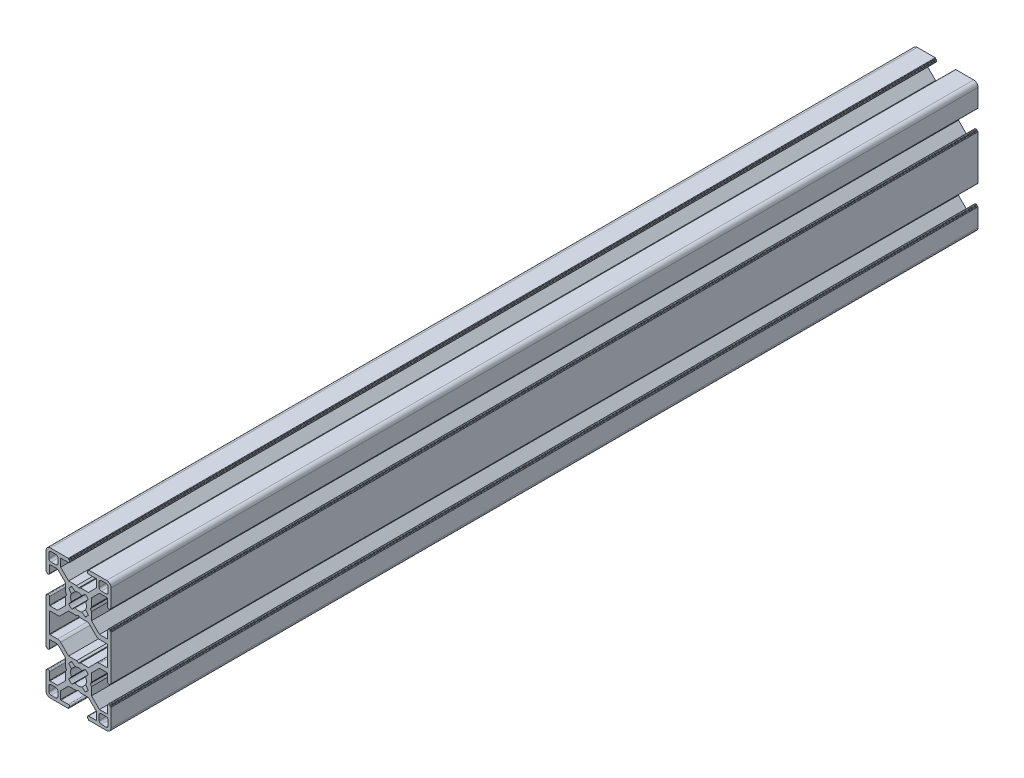
SolidWorks part; units mm, degrees
ref_plane "Спереди" through (0, 0, 0) normal (0, 0, 1) x (1, 0, 0)
ref_plane "Сверху" through (0, 0, 0) normal (0, 1, 0) x (1, 0, 0)
ref_plane "Справа" through (0, 0, 0) normal (1, 0, 0) x (0, 0, -1)
sketch "Эскиз1" plane through (0, 0, 0) normal (0, 0, 1) x (1, 0, 0)
  line L0 (13.4477, 10.8313) -> (13.4477, 8.6313)
  line L1 (10.2477, 7.6313) -> (12.4477, 7.6313)
  line L2 (9.2477, 10.8313) -> (9.2477, 8.6313)
  line L3 (10.2477, 11.8313) -> (12.4477, 11.8313)
  line L4 (2.8836, 2.6497) -> (1.3478, 1.4119)
  line L5 (3.0283, -0.2685) -> (4.2531, 1.286)
  line L6 (5.7522, -0.9686) -> (5.2326, -1.8687)
  line L7 (5.7522, 2.7216) -> (5.7522, -0.9686)
  line L8 (-0.2523, -7.3535) -> (0.6477, -7.8687)
  line L9 (0.6477, -7.8687) -> (4.3335, -7.8687)
  line L15 (14.7477, -27.1187) -> (14.7477, -6.6187)
  line L16 (14.4477, -6.4187) -> (14.5477, -6.4187)
  line L17 (14.2477, -6.2187) -> (14.2477, -6.1187)
  line L18 (13.6977, -5.9187) -> (14.0477, -5.9187)
  line L19 (12.8977, -10.1187) -> (9.4119, -10.1187)
  line L20 (5.7522, -6.4589) -> (5.7522, -2.7687)
  line L21 (5.7522, -2.7687) -> (5.2326, -1.8687)
  line L22 (12.8977, 6.3813) -> (9.4119, 6.3814)
  line L23 (13.6977, 2.1813) -> (14.0477, 2.1813)
  line L24 (14.2477, 2.4813) -> (14.2477, 2.3813)
  line L25 (14.4477, 2.6813) -> (14.5477, 2.6813)
  line L26 (14.7477, 11.1313) -> (14.7477, 2.8813)
  line L27 (4.4977, 13.1313) -> (12.7477, 13.1313)
  line L28 (4.2977, 12.9313) -> (4.2977, 12.8313)
  line L29 (3.9977, 12.6313) -> (4.0977, 12.6313)
  line L30 (3.7977, 12.4313) -> (3.7977, 12.0813)
  line L31 (7.9977, 7.7956) -> (7.9977, 11.2813)
  line L32 (0.6477, 4.1313) -> (4.3335, 4.1313)
  line L33 (-0.2523, 3.6162) -> (0.6477, 4.1313)
  line L38 (-3.3882, -6.3871) -> (-1.8524, -5.1492)
  line L39 (-3.5328, -3.4688) -> (-4.7576, -5.0233)
  line L40 (-0.2523, 3.6162) -> (-1.1523, 4.1313)
  line L41 (-1.1523, 4.1313) -> (-4.8381, 4.1313)
  line L42 (-8.5023, 7.7956) -> (-8.5023, 11.2813)
  line L43 (-4.3023, 12.4313) -> (-4.3023, 12.0813)
  line L44 (-4.5023, 12.6313) -> (-4.6023, 12.6313)
  line L45 (-4.8023, 12.9313) -> (-4.8023, 12.8313)
  line L46 (-5.0023, 13.1313) -> (-13.2523, 13.1313)
  line L47 (-15.2523, 11.1313) -> (-15.2523, 2.8813)
  line L48 (-14.9523, 2.6813) -> (-15.0523, 2.6813)
  line L49 (-14.7523, 2.4813) -> (-14.7523, 2.3813)
  line L50 (-14.2023, 2.1813) -> (-14.5523, 2.1813)
  line L51 (-13.4023, 6.3813) -> (-9.9165, 6.3813)
  line L52 (-6.2567, -2.7687) -> (-5.7371, -1.8687)
  line L53 (-6.2568, -6.4589) -> (-6.2567, -2.7687)
  line L54 (-13.4023, -10.1187) -> (-9.9165, -10.1187)
  line L55 (-14.2023, -5.9187) -> (-14.5523, -5.9187)
  line L56 (-14.7523, -6.2187) -> (-14.7523, -6.1187)
  line L57 (-14.9523, -6.4187) -> (-15.0523, -6.4187)
  line L58 (-15.2523, -27.1187) -> (-15.2523, -6.6187)
  line L63 (3.0283, -3.4688) -> (4.2531, -5.0233)
  line L64 (2.8836, -6.3871) -> (1.3478, -5.1492)
  line L66 (-1.1523, -7.8687) -> (-4.8381, -7.8687)
  line L67 (-0.2523, -7.3535) -> (-1.1523, -7.8687)
  line L72 (-6.2568, 2.7216) -> (-6.2567, -0.9686)
  line L73 (-6.2567, -0.9686) -> (-5.7371, -1.8687)
  line L74 (-3.5328, -0.2685) -> (-4.7576, 1.286)
  line L75 (-3.3882, 2.6497) -> (-1.8524, 1.4119)
  line L76 (-10.7523, 11.8313) -> (-12.9523, 11.8313)
  line L77 (-9.7523, 10.8313) -> (-9.7523, 8.6313)
  line L78 (-10.7523, 7.6313) -> (-12.9523, 7.6313)
  line L79 (-13.9523, 10.8313) -> (-13.9523, 8.6313)
  line L80 (-23.7379, -1.8687) -> (20.6785, -1.8687) construction
  line L81 (-0.2523, 16.0876) -> (-0.2523, -7.3535) construction
  line L82 (25.0447, 11.4813) -> (-23.082, 11.4813) construction
  line L83 (-4.9023, 11.4813) -> (-8.3023, 11.4813)
  line L84 (4.3977, 11.4813) -> (7.7977, 11.4813)
  line L85 (-6.4795, 6.1563) -> (-9.3562, 3.2829) construction
  line L88 (-0.2523, -1.8687) -> (-27.0655, 24.9445) construction
  line L89 (-13.6023, 15.2415) -> (-13.6023, -9.9187) construction
  line L90 (-13.6023, 6.1813) -> (-13.6023, 2.7813)
  line L91 (-13.6023, -6.5187) -> (-13.6023, -9.9187)
  line L92 (12.8977, -12.1187) -> (9.4119, -12.1187)
  line L93 (13.0977, -6.5187) -> (13.0977, -9.9187)
  line L94 (13.0977, 6.1813) -> (13.0977, 2.7813)
  line L95 (-21.3718, 20.6651) -> (-9.2608, 8.554) construction
  line L96 (-23.3389, 19.8037) -> (-10.4618, 6.9266) construction
  line L97 (-4.8381, 4.1313) -> (-8.5023, 7.7956)
  line L98 (-9.9165, 6.3813) -> (-6.2568, 2.7216)
  line L99 (-8.5023, 7.7956) -> (-4.8381, 4.1313) construction
  line L100 (-3.8605, 3.1538) -> (4.017, -4.7238) construction
  line L101 (-9.9165, 6.3813) -> (-6.2568, 2.7216) construction
  line L102 (-4.5216, 0.9864) -> (4.3047, -7.8399) construction
  line L103 (-0.2523, -1.8687) -> (27.0655, 25.4491) construction
  line L104 (7.9977, -11.5329) -> (4.3335, -7.8687)
  line L105 (5.7522, -6.4589) -> (9.4119, -10.1187)
  line L106 (5.7522, -6.4589) -> (10.6619, -11.3687) construction
  line L107 (4.3335, -7.8687) -> (9.2477, -12.7829) construction
  line L108 (9.4119, 6.3814) -> (5.7522, 2.7216)
  line L109 (4.3335, 4.1313) -> (7.9977, 7.7956)
  line L110 (-9.9165, -10.1187) -> (-6.2568, -6.4589)
  line L111 (-4.8381, -7.8687) -> (-8.5023, -11.5329)
  line L112 (4.3335, -25.8687) -> (12.0335, -18.1687) construction
  line L113 (5.7522, -27.2784) -> (10.6619, -22.3687) construction
  line L114 (-0.2523, -31.8687) -> (27.0655, -59.1864) construction
  line L115 (-4.5216, -34.7238) -> (4.3047, -25.8975) construction
  line L116 (-9.9165, -40.1187) -> (-6.2568, -36.4589) construction
  line L117 (-3.8605, -36.8911) -> (4.017, -29.0136) construction
  line L118 (-8.5023, -41.5329) -> (-4.8381, -37.8687) construction
  line L119 (-23.3389, -53.5411) -> (-10.4618, -40.6639) construction
  line L120 (-21.3718, -54.4024) -> (-9.2608, -42.2913) construction
  line L121 (-13.4023, -21.6187) -> (-9.9165, -21.6187)
  line L122 (-13.6023, -48.9788) -> (-13.6023, -23.6187) construction
  line L123 (-0.2523, -31.8687) -> (-27.0655, -58.6818) construction
  line L124 (-6.4795, -39.8937) -> (-9.3562, -37.0202) construction
  line L125 (25.0447, -45.2187) -> (-23.082, -45.2187) construction
  line L126 (-0.2523, -49.825) -> (-0.2523, -26.3838) construction
  line L127 (-23.7379, -31.8687) -> (20.6785, -31.8687) construction
  line L128 (-4.8381, -25.8687) -> (-8.5023, -22.2044)
  line L129 (-9.9165, -23.6187) -> (-6.2568, -27.2784)
  line L130 (4.3335, -37.8687) -> (7.9977, -41.5329)
  line L131 (9.4119, -40.1187) -> (5.7522, -36.4589)
  line L132 (5.7522, -27.2784) -> (9.4119, -23.6187)
  line L133 (7.9977, -22.2044) -> (4.3335, -25.8687)
  line L134 (-9.9165, -40.1187) -> (-6.2568, -36.4589)
  line L135 (-4.8381, -37.8687) -> (-8.5023, -41.5329)
  line L136 (13.0977, -39.9187) -> (13.0977, -36.5187)
  line L137 (13.0977, -27.2187) -> (13.0977, -23.8187)
  line L138 (-13.6023, -27.2187) -> (-13.6023, -23.8187)
  line L139 (-13.6023, -39.9187) -> (-13.6023, -36.5187)
  line L141 (9.4119, -21.6187) -> (12.8977, -21.6187)
  line L142 (4.3977, -45.2187) -> (7.7977, -45.2187)
  line L143 (-4.9023, -45.2187) -> (-8.3023, -45.2187)
  line L144 (-13.9523, -44.5687) -> (-13.9523, -42.3687)
  line L145 (-10.7523, -41.3687) -> (-12.9523, -41.3687)
  line L146 (-9.7523, -44.5687) -> (-9.7523, -42.3687)
  line L147 (-10.7523, -45.5687) -> (-12.9523, -45.5687)
  line L148 (-3.3882, -36.3871) -> (-1.8524, -35.1492)
  line L149 (-3.5328, -33.4688) -> (-4.7576, -35.0233)
  line L150 (-6.2567, -32.7687) -> (-5.7371, -31.8687)
  line L151 (-6.2568, -36.4589) -> (-6.2567, -32.7687)
  line L156 (-0.2523, -26.3838) -> (-1.1523, -25.8687)
  line L157 (-1.1523, -25.8687) -> (-4.8381, -25.8687)
  line L158 (-13.6023, -12.3187) -> (-13.6023, -21.4187)
  line L159 (2.8836, -27.3503) -> (1.3478, -28.5881)
  line L160 (3.0283, -30.2685) -> (4.2531, -28.714)
  line L161 (-9.9165, -12.1187) -> (-13.4023, -12.1187)
  line L162 (13.0977, -12.3187) -> (13.0977, -21.4187)
  line L165 (-14.9523, -27.3187) -> (-15.0523, -27.3187)
  line L166 (-14.7523, -27.5187) -> (-14.7523, -27.6187)
  line L167 (-14.2023, -27.8187) -> (-14.5523, -27.8187)
  line L168 (-13.4023, -23.6187) -> (-9.9165, -23.6187)
  line L169 (-6.2568, -27.2784) -> (-6.2567, -30.9686)
  line L170 (-6.2567, -30.9686) -> (-5.7371, -31.8687)
  line L171 (-13.4023, -40.1187) -> (-9.9165, -40.1187)
  line L172 (-14.2023, -35.9187) -> (-14.5523, -35.9187)
  line L173 (-14.7523, -36.2187) -> (-14.7523, -36.1187)
  line L174 (-14.9523, -36.4187) -> (-15.0523, -36.4187)
  line L175 (-15.2523, -44.8687) -> (-15.2523, -36.6187)
  line L176 (-5.0023, -46.8687) -> (-13.2523, -46.8687)
  line L177 (-4.8023, -46.6687) -> (-4.8023, -46.5687)
  line L178 (-4.5023, -46.3687) -> (-4.6023, -46.3687)
  line L179 (-4.3023, -46.1687) -> (-4.3023, -45.8187)
  line L180 (-8.5023, -41.5329) -> (-8.5023, -45.0187)
  line L181 (-1.1523, -37.8687) -> (-4.8381, -37.8687)
  line L182 (-0.2523, -37.3535) -> (-1.1523, -37.8687)
  line L183 (-3.5328, -30.2685) -> (-4.7576, -28.714)
  line L184 (-3.3882, -27.3503) -> (-1.8524, -28.5881)
  line L189 (-0.2523, -37.3535) -> (0.6477, -37.8687)
  line L190 (0.6477, -37.8687) -> (4.3335, -37.8687)
  line L191 (7.9977, -41.5329) -> (7.9977, -45.0187)
  line L192 (3.7977, -46.1687) -> (3.7977, -45.8187)
  line L193 (3.9977, -46.3687) -> (4.0977, -46.3687)
  line L194 (4.2977, -46.6687) -> (4.2977, -46.5687)
  line L195 (4.4977, -46.8687) -> (12.7477, -46.8687)
  line L196 (14.7477, -44.8687) -> (14.7477, -36.6187)
  line L197 (14.4477, -36.4187) -> (14.5477, -36.4187)
  line L198 (14.2477, -36.2187) -> (14.2477, -36.1187)
  line L199 (13.6977, -35.9187) -> (14.0477, -35.9187)
  line L200 (12.8977, -40.1187) -> (9.4119, -40.1187)
  line L201 (5.7522, -30.9686) -> (5.2326, -31.8687)
  line L202 (5.7522, -27.2784) -> (5.7522, -30.9686)
  line L203 (12.8977, -23.6187) -> (9.4119, -23.6187)
  line L204 (13.6977, -27.8187) -> (14.0477, -27.8187)
  line L205 (14.2477, -27.5187) -> (14.2477, -27.6187)
  line L206 (14.4477, -27.3187) -> (14.5477, -27.3187)
  line L212 (0.6477, -25.8687) -> (4.3335, -25.8687)
  line L213 (-0.2523, -26.3838) -> (0.6477, -25.8687)
  line L214 (5.7522, -36.4589) -> (5.7522, -32.7687)
  line L215 (5.7522, -32.7687) -> (5.2326, -31.8687)
  line L216 (3.0283, -33.4688) -> (4.2531, -35.0233)
  line L217 (2.8836, -36.3871) -> (1.3478, -35.1492)
  line L218 (10.2477, -45.5687) -> (12.4477, -45.5687)
  line L219 (9.2477, -44.5687) -> (9.2477, -42.3687)
  line L220 (10.2477, -41.3687) -> (12.4477, -41.3687)
  line L221 (13.4477, -44.5687) -> (13.4477, -42.3687)
  arc A0 (13.4477, 10.8313) -> (12.4477, 11.8313) centre (12.4477, 10.8313) ccw
  arc A1 (12.4477, 7.6313) -> (13.4477, 8.6313) centre (12.4477, 8.6313) ccw
  arc A2 (9.2477, 8.6313) -> (10.2477, 7.6313) centre (10.2477, 8.6313) ccw
  arc A3 (10.2477, 11.8313) -> (9.2477, 10.8313) centre (10.2477, 10.8313) ccw
  arc A4 (1.3478, 1.4119) -> (-1.8524, 1.4119) centre (-0.2523, -1.8687) ccw
  arc A9 (14.7477, -6.6187) -> (14.5477, -6.4187) centre (14.5477, -6.6187) ccw
  arc A10 (14.4477, -6.4187) -> (14.2477, -6.2187) centre (14.4477, -6.2187) cw
  arc A11 (14.2477, -6.1187) -> (14.0477, -5.9187) centre (14.0477, -6.1187) ccw
  arc A12 (4.2531, 1.286) -> (2.8836, 2.6497) centre (-0.2523, -1.8687) ccw
  arc A13 (14.2477, 2.3813) -> (14.0477, 2.1813) centre (14.0477, 2.3813) cw
  arc A14 (14.4477, 2.6813) -> (14.2477, 2.4813) centre (14.4477, 2.4813) ccw
  arc A15 (14.7477, 2.8813) -> (14.5477, 2.6813) centre (14.5477, 2.8813) cw
  arc A16 (12.7477, 13.1313) -> (14.7477, 11.1313) centre (12.7477, 11.1313) cw
  arc A17 (4.2977, 12.9313) -> (4.4977, 13.1313) centre (4.4977, 12.9313) cw
  arc A18 (4.0977, 12.6313) -> (4.2977, 12.8313) centre (4.0977, 12.8313) ccw
  arc A19 (3.7977, 12.4313) -> (3.9977, 12.6313) centre (3.9977, 12.4313) cw
  arc A24 (-4.7576, -5.0233) -> (-3.3882, -6.3871) centre (-0.2523, -1.8687) ccw
  arc A25 (-3.5328, -0.2685) -> (-3.5328, -3.4688) centre (-0.2523, -1.8687) ccw
  arc A26 (-4.3023, 12.4313) -> (-4.5023, 12.6313) centre (-4.5023, 12.4313) ccw
  arc A27 (-4.6023, 12.6313) -> (-4.8023, 12.8313) centre (-4.6023, 12.8313) cw
  arc A28 (-4.8023, 12.9313) -> (-5.0023, 13.1313) centre (-5.0023, 12.9313) ccw
  arc A29 (-13.2523, 13.1313) -> (-15.2523, 11.1313) centre (-13.2523, 11.1313) ccw
  arc A30 (-15.2523, 2.8813) -> (-15.0523, 2.6813) centre (-15.0523, 2.8813) ccw
  arc A31 (-14.9523, 2.6813) -> (-14.7523, 2.4813) centre (-14.9523, 2.4813) cw
  arc A32 (-14.7523, 2.3813) -> (-14.5523, 2.1813) centre (-14.5523, 2.3813) ccw
  arc A33 (-4.7576, 1.286) -> (-3.3882, 2.6497) centre (-0.2523, -1.8687) cw
  arc A34 (-14.7523, -6.1187) -> (-14.5523, -5.9187) centre (-14.5523, -6.1187) cw
  arc A35 (3.0283, -0.2685) -> (3.0283, -3.4688) centre (-0.2523, -1.8687) cw
  arc A36 (4.2531, -5.0233) -> (2.8836, -6.3871) centre (-0.2523, -1.8687) cw
  arc A37 (1.3478, -5.1492) -> (-1.8524, -5.1492) centre (-0.2523, -1.8687) cw
  arc A38 (-14.9523, -6.4187) -> (-14.7523, -6.2187) centre (-14.9523, -6.2187) ccw
  arc A39 (-15.2523, -6.6187) -> (-15.0523, -6.4187) centre (-15.0523, -6.6187) cw
  arc A48 (-10.7523, 11.8313) -> (-9.7523, 10.8313) centre (-10.7523, 10.8313) cw
  arc A49 (-9.7523, 8.6313) -> (-10.7523, 7.6313) centre (-10.7523, 8.6313) cw
  arc A50 (-12.9523, 7.6313) -> (-13.9523, 8.6313) centre (-12.9523, 8.6313) cw
  arc A51 (-13.9523, 10.8313) -> (-12.9523, 11.8313) centre (-12.9523, 10.8313) cw
  arc A52 (-8.5023, 11.2813) -> (-8.3023, 11.4813) centre (-8.3023, 11.2813) cw
  arc A53 (-4.9023, 11.4813) -> (-4.3023, 12.0813) centre (-4.9023, 12.0813) ccw
  arc A54 (4.3977, 11.4813) -> (3.7977, 12.0813) centre (4.3977, 12.0813) cw
  arc A55 (7.9977, 11.2813) -> (7.7977, 11.4813) centre (7.7977, 11.2813) ccw
  arc A60 (-14.2023, 2.1813) -> (-13.6023, 2.7813) centre (-14.2023, 2.7813) ccw
  arc A61 (-13.6023, 6.1813) -> (-13.4023, 6.3813) centre (-13.4023, 6.1813) cw
  arc A62 (-13.4023, -10.1187) -> (-13.6023, -9.9187) centre (-13.4023, -9.9187) cw
  arc A63 (-13.6023, -6.5187) -> (-14.2023, -5.9187) centre (-14.2023, -6.5187) ccw
  arc A64 (12.8977, -10.1187) -> (13.0977, -9.9187) centre (12.8977, -9.9187) ccw
  arc A65 (13.0977, -6.5187) -> (13.6977, -5.9187) centre (13.6977, -6.5187) cw
  arc A66 (13.6977, 2.1813) -> (13.0977, 2.7813) centre (13.6977, 2.7813) cw
  arc A67 (13.0977, 6.1813) -> (12.8977, 6.3813) centre (12.8977, 6.1813) ccw
  arc A68 (13.0977, -39.9187) -> (12.8977, -40.1187) centre (12.8977, -39.9187) cw
  arc A69 (13.6977, -35.9187) -> (13.0977, -36.5187) centre (13.6977, -36.5187) ccw
  arc A70 (13.0977, -27.2187) -> (13.6977, -27.8187) centre (13.6977, -27.2187) ccw
  arc A71 (12.8977, -23.6187) -> (13.0977, -23.8187) centre (12.8977, -23.8187) cw
  arc A72 (-13.6023, -27.2187) -> (-14.2023, -27.8187) centre (-14.2023, -27.2187) cw
  arc A73 (-13.4023, -23.6187) -> (-13.6023, -23.8187) centre (-13.4023, -23.8187) ccw
  arc A74 (-13.6023, -39.9187) -> (-13.4023, -40.1187) centre (-13.4023, -39.9187) ccw
  arc A75 (-14.2023, -35.9187) -> (-13.6023, -36.5187) centre (-14.2023, -36.5187) cw
  arc A76 (9.4119, -12.1187) -> (7.9977, -11.5329) centre (9.4119, -10.1187) cw
  arc A77 (-9.9165, -12.1187) -> (-8.5023, -11.5329) centre (-9.9165, -10.1187) ccw
  arc A78 (-9.9165, -21.6187) -> (-8.5023, -22.2044) centre (-9.9165, -23.6187) cw
  arc A79 (7.9977, -22.2044) -> (9.4119, -21.6187) centre (9.4119, -23.6187) cw
  arc A80 (7.9977, -45.0187) -> (7.7977, -45.2187) centre (7.7977, -45.0187) cw
  arc A81 (4.3977, -45.2187) -> (3.7977, -45.8187) centre (4.3977, -45.8187) ccw
  arc A82 (-4.9023, -45.2187) -> (-4.3023, -45.8187) centre (-4.9023, -45.8187) cw
  arc A83 (-8.5023, -45.0187) -> (-8.3023, -45.2187) centre (-8.3023, -45.0187) ccw
  arc A84 (-13.9523, -44.5687) -> (-12.9523, -45.5687) centre (-12.9523, -44.5687) ccw
  arc A85 (-12.9523, -41.3687) -> (-13.9523, -42.3687) centre (-12.9523, -42.3687) ccw
  arc A86 (-9.7523, -42.3687) -> (-10.7523, -41.3687) centre (-10.7523, -42.3687) ccw
  arc A87 (-10.7523, -45.5687) -> (-9.7523, -44.5687) centre (-10.7523, -44.5687) ccw
  arc A88 (-13.6023, -21.4187) -> (-13.4023, -21.6187) centre (-13.4023, -21.4187) ccw
  arc A89 (-13.6023, -12.3187) -> (-13.4023, -12.1187) centre (-13.4023, -12.3187) cw
  arc A94 (13.0977, -12.3187) -> (12.8977, -12.1187) centre (12.8977, -12.3187) ccw
  arc A96 (-15.2523, -27.1187) -> (-15.0523, -27.3187) centre (-15.0523, -27.1187) ccw
  arc A97 (-14.9523, -27.3187) -> (-14.7523, -27.5187) centre (-14.9523, -27.5187) cw
  arc A98 (1.3478, -28.5881) -> (-1.8524, -28.5881) centre (-0.2523, -31.8687) ccw
  arc A99 (4.2531, -28.714) -> (2.8836, -27.3503) centre (-0.2523, -31.8687) ccw
  arc A100 (3.0283, -33.4688) -> (3.0283, -30.2685) centre (-0.2523, -31.8687) ccw
  arc A101 (-14.7523, -27.6187) -> (-14.5523, -27.8187) centre (-14.5523, -27.6187) ccw
  arc A102 (-4.7576, -35.0233) -> (-3.3882, -36.3871) centre (-0.2523, -31.8687) ccw
  arc A103 (-14.7523, -36.1187) -> (-14.5523, -35.9187) centre (-14.5523, -36.1187) cw
  arc A104 (-14.9523, -36.4187) -> (-14.7523, -36.2187) centre (-14.9523, -36.2187) ccw
  arc A105 (-15.2523, -36.6187) -> (-15.0523, -36.4187) centre (-15.0523, -36.6187) cw
  arc A106 (-13.2523, -46.8687) -> (-15.2523, -44.8687) centre (-13.2523, -44.8687) cw
  arc A107 (-4.8023, -46.6687) -> (-5.0023, -46.8687) centre (-5.0023, -46.6687) cw
  arc A108 (-4.6023, -46.3687) -> (-4.8023, -46.5687) centre (-4.6023, -46.5687) ccw
  arc A109 (-4.3023, -46.1687) -> (-4.5023, -46.3687) centre (-4.5023, -46.1687) cw
  arc A110 (-3.5328, -33.4688) -> (-3.5328, -30.2685) centre (-0.2523, -31.8687) cw
  arc A111 (-4.7576, -28.714) -> (-3.3882, -27.3503) centre (-0.2523, -31.8687) cw
  arc A116 (3.7977, -46.1687) -> (3.9977, -46.3687) centre (3.9977, -46.1687) ccw
  arc A117 (4.0977, -46.3687) -> (4.2977, -46.5687) centre (4.0977, -46.5687) cw
  arc A118 (4.2977, -46.6687) -> (4.4977, -46.8687) centre (4.4977, -46.6687) ccw
  arc A119 (12.7477, -46.8687) -> (14.7477, -44.8687) centre (12.7477, -44.8687) ccw
  arc A120 (14.7477, -36.6187) -> (14.5477, -36.4187) centre (14.5477, -36.6187) ccw
  arc A121 (14.4477, -36.4187) -> (14.2477, -36.2187) centre (14.4477, -36.2187) cw
  arc A122 (14.2477, -36.1187) -> (14.0477, -35.9187) centre (14.0477, -36.1187) ccw
  arc A123 (4.2531, -35.0233) -> (2.8836, -36.3871) centre (-0.2523, -31.8687) cw
  arc A124 (14.2477, -27.6187) -> (14.0477, -27.8187) centre (14.0477, -27.6187) cw
  arc A125 (14.4477, -27.3187) -> (14.2477, -27.5187) centre (14.4477, -27.5187) ccw
  arc A126 (14.7477, -27.1187) -> (14.5477, -27.3187) centre (14.5477, -27.1187) cw
  arc A128 (12.8977, -21.6187) -> (13.0977, -21.4187) centre (12.8977, -21.4187) ccw
  arc A131 (1.3478, -35.1492) -> (-1.8524, -35.1492) centre (-0.2523, -31.8687) cw
  arc A132 (10.2477, -45.5687) -> (9.2477, -44.5687) centre (10.2477, -44.5687) cw
  arc A133 (9.2477, -42.3687) -> (10.2477, -41.3687) centre (10.2477, -42.3687) cw
  arc A134 (12.4477, -41.3687) -> (13.4477, -42.3687) centre (12.4477, -42.3687) cw
  arc A135 (13.4477, -44.5687) -> (12.4477, -45.5687) centre (12.4477, -44.5687) cw
  point P81 (14.7477, 13.1313)
  point P82 (-0.2523, 13.1313)
  point P202 (-0.2523, -1.8687)
  point P203 (14.7477, -1.8687)
  point P215 (-15.2523, -1.8687)
  point P216 (-15.2523, -16.8687)
  point P217 (-15.2523, 13.1313)
  point P503 (-15.2523, -46.8687)
  point P504 (-15.2523, -31.8687)
  point P505 (14.7477, -31.8687)
  point P506 (-0.2523, -31.8687)
  point P507 (-0.2523, -46.8687)
  point P508 (14.7477, -46.8687)
  dimension "D6" = 7.3
  dimension "D7" = 11
  dimension "D10" = 0.2
  dimension "D11" = 0.6
  dimension "D14" = 0.6
  dimension "D15" = 0.2
  dimension "D16" = 2
  dimension "D17" = 0.6
  dimension "D5" = 2
  dimension "D13" = 2
  dimension "D21" = 2
  dimension "D22" = 2
  dimension "D23" = 0.2
  dimension "D24" = 0.2
  dimension "D25" = 0.2
  dimension "D26" = 0.2
  dimension "D3" = 2
  dimension "D4" = 8.1
  dimension "D8" = 8.1
  dimension "D9" = 1.65
  dimension "D12" = 45
  dimension "D18" = 1
  dimension "D19" = 1
  dimension "D20" = 45
extrude "Бобышка-Вытянуть1" add sketch "Эскиз1" along normal blind 400
